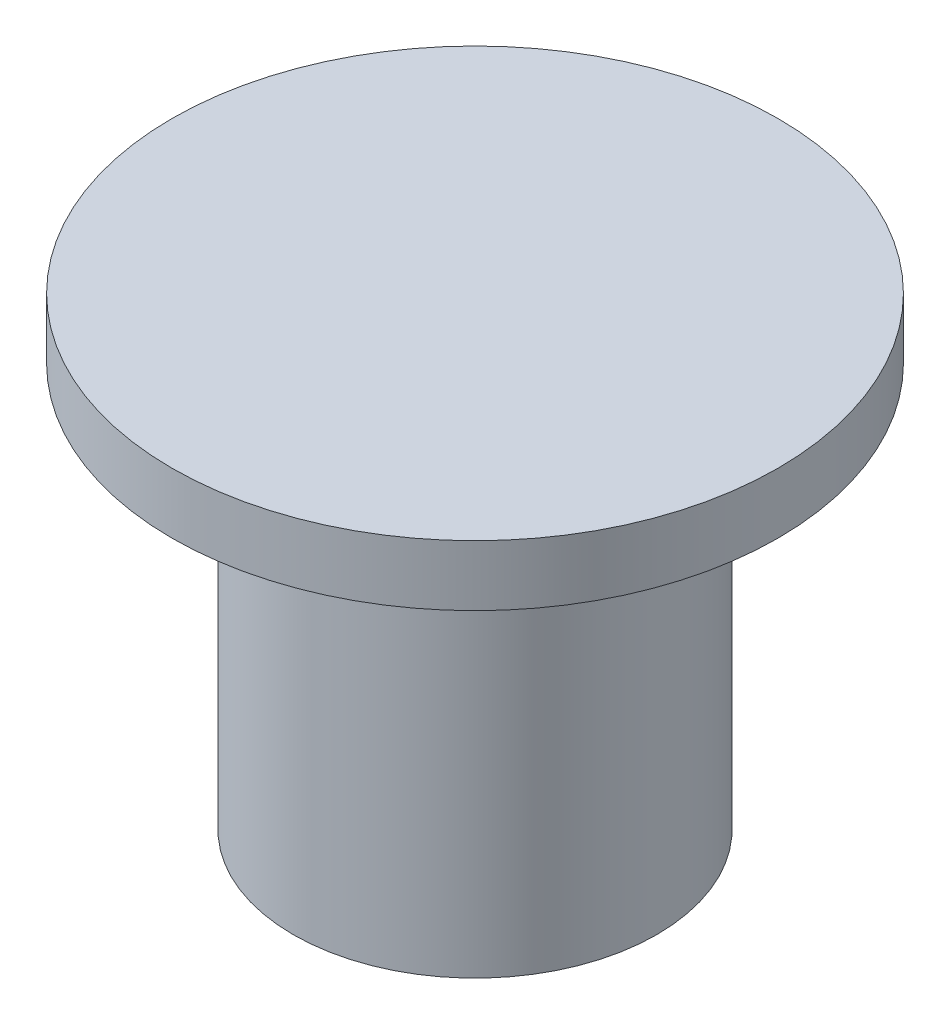
SolidWorks part; units mm, degrees
ref_plane "Alzado" through (0, 0, 0) normal (0, 0, 1) x (1, 0, 0)
ref_plane "Planta" through (0, 0, 0) normal (0, 1, 0) x (1, 0, 0)
ref_plane "Vista lateral" through (0, 0, 0) normal (1, 0, 0) x (0, 0, -1)
sketch "Croquis1" plane through (0, 0, 0) normal (0, 0, 1) x (1, 0, 0)
  line L0 (-79.5372, 27.6748) -> (-87.0372, 27.6748)
  line L1 (-87.0372, 27.6748) -> (-87.0372, 26.1748)
  line L2 (-87.0372, 26.1748) -> (-84.0372, 26.1748)
  line L3 (-83.0372, 26.1748) -> (-83.0372, 16.1748)
  line L4 (-84.0372, 26.1748) -> (-84.0372, 16.1748)
  line L5 (-84.0372, 16.1748) -> (-83.0372, 16.1748)
  line L6 (-83.0372, 26.1748) -> (-79.5372, 26.1748)
  line L7 (-79.5372, 26.1748) -> (-79.5372, 27.6748)
revolve "Revolución1" add sketch "Croquis1" angle 360 about L7
